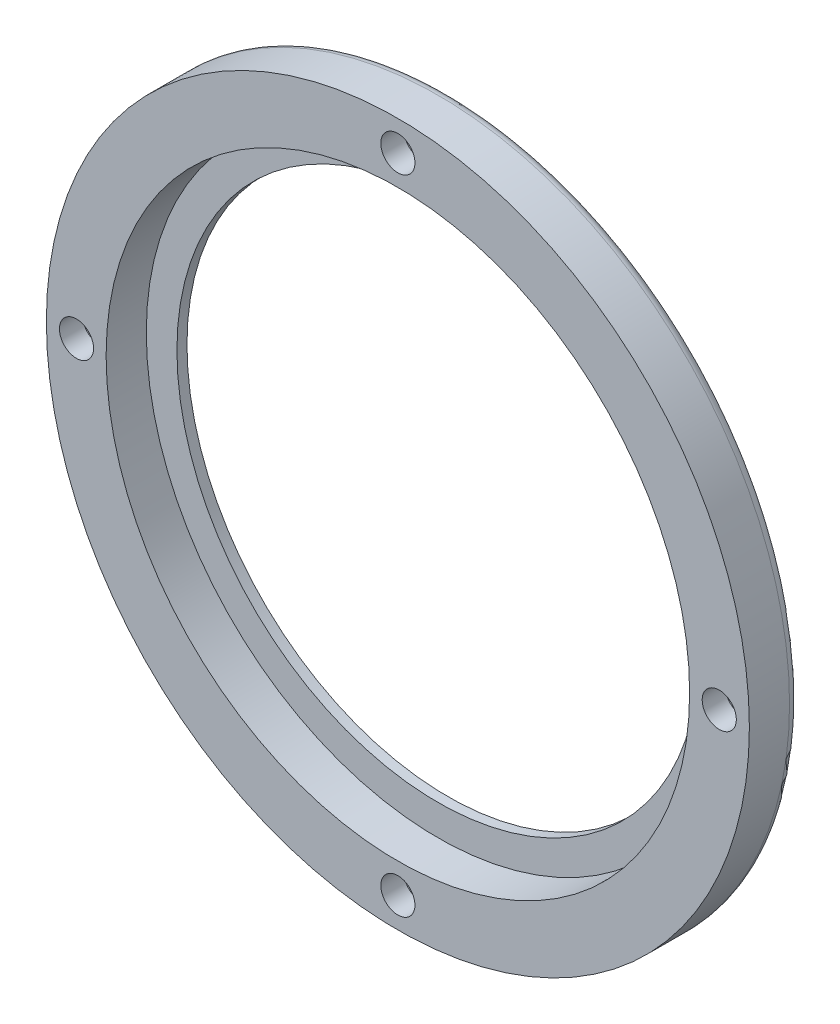
SolidWorks part; units mm, degrees
ref_plane "前视基准面" through (0, 0, 0) normal (0, 0, 1) x (1, 0, 0)
ref_plane "上视基准面" through (0, 0, 0) normal (0, 1, 0) x (1, 0, 0)
ref_plane "右视基准面" through (0, 0, 0) normal (1, 0, 0) x (0, 0, -1)
sketch "草图1" plane through (0, 0, 0) normal (0, 1, 0) x (1, 0, 0)
  line L0 (35, 29) -> (0, 29)
  line L1 (0, 29) -> (0, 24)
  line L2 (0, 24) -> (35, 24)
  line L3 (35, 24) -> (35, 29)
  line L4 (0, 29) -> (0, 24) construction
revolve "旋转1" add sketch "草图1" angle 360 about L4
hole_wizard "Ø3.4 (3.4) 直径孔1" positions "草图11" profile "草图10" hole size "Ø3.4" standard "ANSI Metric"
sketch "草图11" plane through (0, 0, -29) normal (0, 0, -1) x (-1, 0, 0)
  point P0 (0, -32)
  point P1 (-32, 0)
  point P2 (0, 32)
  point P3 (32, 0)
sketch "草图10" plane through (0, -32, -29) normal (1, 0, 0) x (0, 1, 0)
  line L0 (0, 0) -> (0, 5)
  line L1 (0, 5) -> (1.7, 5)
  line L2 (1.7, 5) -> (1.7, 0)
  line L5 (1.7, 0) -> (0, 0)
  line L11 (0, -6.35) -> (0, 107.95) construction
  dimension "通孔孔直径" = 3.4
  dimension "通孔孔深度" = 5
hole_wizard "M48 六角头螺栓的柱形沉头孔1" positions "草图15" profile "草图14" counterbore size "M48" standard "ANSI Metric"
sketch "草图15" plane through (0, 0, -24) normal (0, 0, 1) x (1, 0, 0)
  point P0 (0, 0)
sketch "草图14" plane through (0, 0, -24) normal (1, 0, 0) x (0, -1, 0)
  line L0 (0, 0) -> (0, 5)
  line L1 (0, 5) -> (26, 5)
  line L3 (26, 5) -> (26, 4)
  line L4 (26, 4) -> (29.05, 4)
  line L5 (29.05, 4) -> (29.05, 0)
  line L7 (29.05, 0) -> (0, 0)
  line L11 (0, -6.35) -> (0, 107.95) construction
  dimension "通孔孔直径" = 52
  dimension "通孔孔深度" = 5
  dimension "柱形沉头孔直径" = 58.1
  dimension "柱形沉头孔深度" = 4
fillet "圆角1" radius 1 1 edges at (35, 0, -29)
sketch "草图17" plane through (0, 0, -29) normal (0, 0, -1) x (-1, 0, 0)
  circle A0 centre (0, -32) radius 2.8
  circle A1 centre (-32, 0) radius 2.8
  circle A2 centre (0, 32) radius 2.8
  circle A3 centre (32, 0) radius 2.8
  point P12 (0, 0)
  dimension "D1" = 4
extrude "切除-拉伸9" cut sketch "草图17" against normal blind 2.7
